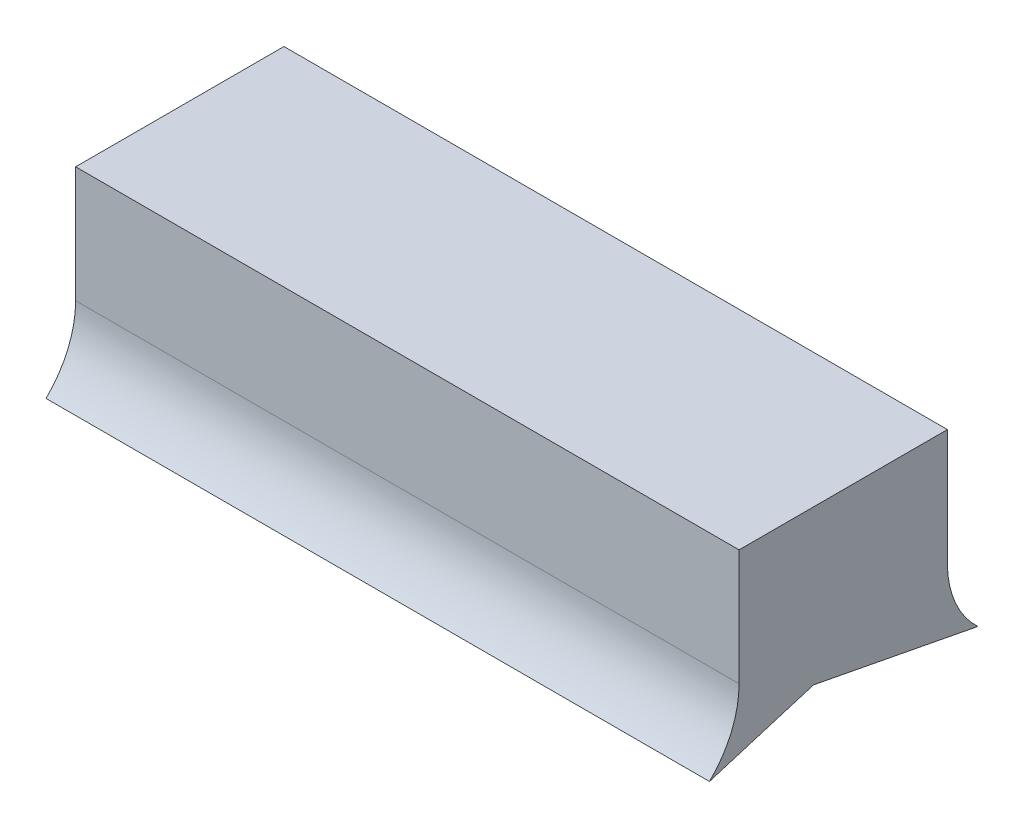
SolidWorks part; units mm, degrees
ref_plane "Front Plane" through (0, 0, 0) normal (0, 0, 1) x (1, 0, 0)
ref_plane "Top Plane" through (0, 0, 0) normal (0, 1, 0) x (1, 0, 0)
ref_plane "Right Plane" through (0, 0, 0) normal (1, 0, 0) x (0, 0, -1)
sketch "Sketch3" plane through (328.8714, 0, 0) normal (1, 0, 0) x (0, 0, -1)
  line L0 (62.3974, 31.4942) -> (63.199, 29.6619) construction
  line L1 (171.8643, 15.752) -> (170.1388, 16.7632) construction
  line L2 (101.8016, 13.8733) -> (138.9368, 27.3894) construction
  line L3 (138.9368, 27.3894) -> (176.072, 13.8733) construction
  line L10 (138.9368, 27.3894) -> (138.9368, 69.1542) construction
  line L12 (114.4617, 69.1542) -> (126.199, 69.1542) construction
  line L19 (121.1864, 69.1542) -> (121.1864, 41.5042)
  line L20 (114.1206, 24.8542) -> (138.9368, 32.3894)
  line L21 (138.9368, 32.3894) -> (178.1563, 24.8542)
  line L22 (170.8621, 69.1542) -> (170.8621, 41.5042)
  line L23 (162.9362, 69.1542) -> (209.4617, 69.1542) construction
  line L24 (119.6864, 69.1542) -> (119.6864, 41.5042) construction
  line L25 (171.8621, 69.1542) -> (171.8621, 41.5042) construction
  line L26 (121.1864, 69.1542) -> (170.8621, 69.1542)
  circle A0 centre (91.199, 43.0038) radius 31 construction
  circle A1 centre (186.6746, 43.0038) radius 31 construction
  arc A2 (121.1864, 41.5042) -> (114.1206, 24.8542) centre (98.0364, 41.5042) cw
  arc A3 (170.8621, 41.5042) -> (178.1563, 24.8542) centre (193.5121, 41.5042) ccw
  arc A5 (76.3864, 41.5042) -> (119.6864, 41.5042) centre (98.0364, 41.5042) ccw construction
  arc A7 (171.8621, 41.5042) -> (215.1621, 41.5042) centre (193.5121, 41.5042) ccw construction
  point P46 (193.5121, 19.8542)
  dimension "D1" = 140
  dimension "D2" = 1.5
  dimension "D3" = 1
  dimension "D4" = 5
  dimension "D5" = 5
extrude "Boss-Extrude1" add sketch "Sketch3" against normal up to surface (158.2 mm away)
equation "\"D1@Sketch3\"=180-40"
